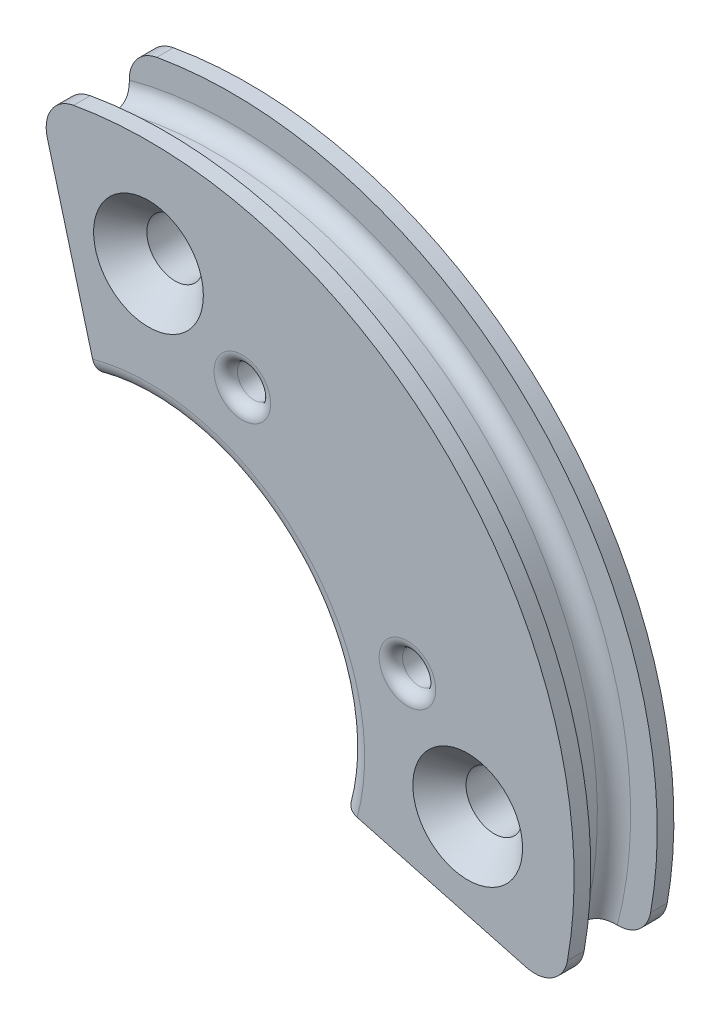
SolidWorks part; units mm, degrees
ref_plane "Front" through (0, 0, 0) normal (0, 0, 1) x (1, 0, 0)
ref_plane "Top" through (0, 0, 0) normal (0, 1, 0) x (1, 0, 0)
ref_plane "Right" through (0, 0, 0) normal (1, 0, 0) x (0, 0, -1)
sketch "Sketch1" plane through (0, 0, 0) normal (0, 0, 1) x (1, 0, 0)
  circle A2 centre (9.6, 0) radius 0.85
  circle A24 centre (0, 0) radius 12
  circle A25 centre (0, 0) radius 6
  circle A30 centre (0, -9.6) radius 0.85
  circle A32 centre (-9.6, 0) radius 0.85
  circle A34 centre (0, 9.6) radius 0.85
  point P20 (0, 0)
  dimension "D1" = 4
  dimension "D2" = 24
  dimension "D3" = 12
  dimension "D4" = 19.2
  dimension "D5" = 1.7
extrude "Boss-Extrude1" add sketch "Sketch1" along normal mid plane 3
sketch "Sketch2" plane through (0, 0, 0) normal (0, 1, 0) x (1, 0, 0)
  line L1 (0, 0) -> (0, 3.24) construction
  line L3 (-11.5, 0.5) -> (-11.5, -0.5)
  line L4 (-11.5, 0) -> (-12, 0) construction
  line L5 (-12, -1) -> (-12, 1)
  line L6 (-12, 1.5) -> (-12, -1.5) construction
  arc A1 (-12, 1) -> (-11.5, 0.5) centre (-12, 0.5) cw
  arc A2 (-12, -1) -> (-11.5, -0.5) centre (-12, -0.5) ccw
  dimension "D1" = 23
  dimension "D2" = 2
revolve "Cut-Revolve1" cut sketch "Sketch2" angle 360 about L1
sketch "Sketch6" plane through (0, 0, 0) normal (0, 1, 0) x (1, 0, 0)
  line L0 (0, 0) -> (15.0491, 0) construction
  line L1 (12, 1.5) -> (12.8, 1.5)
  line L2 (12, 1.5) -> (12, 1)
  line L3 (12, 1) -> (12.8, 1)
  line L4 (12.8, 1.5) -> (12.8, 1)
  line L5 (12.8, -1.5) -> (12.8, -1)
  line L6 (12, -1) -> (12.8, -1)
  line L7 (12, -1.5) -> (12, -1)
  line L8 (12, -1.5) -> (12.8, -1.5)
  line L9 (12, -1) -> (-12, -1) construction
  line L10 (0, 0) -> (0, 2.8804) construction
  arc A0 (11.5, -0.5) -> (12, -1) centre (12, -0.5) ccw construction
  dimension "D1" = 0.8
revolve "Revolve1" add sketch "Sketch6" angle 360 about L10
sketch "Sketch4" plane through (0, 0, 0) normal (0, 0, 1) x (1, 0, 0)
  line L0 (-3.7436, 13.9714) -> (0, 0)
  line L1 (0, 0) -> (8.4853, 8.4853) construction
  line L2 (0, 0) -> (-16.6927, 0) construction
  line L3 (14.9002, -3.9925) -> (0, 0)
  line L5 (-3.7436, 13.9714) -> (-15.1881, 13.9714)
  line L6 (-15.1881, 13.9714) -> (-15.1881, -14.8394)
  line L7 (-15.1881, -14.8394) -> (14.9002, -14.8394)
  line L10 (14.9002, -3.9925) -> (14.9002, -14.8394)
  point P15 (11.5911, -3.1058)
  point P18 (-3.1058, 11.5911)
  dimension "D3" = 60
  dimension "D1" = 135
  dimension "D2" = 120
extrude "Cut-Extrude1" cut sketch "Sketch4" against normal through all both and the other way through all
sketch "Sketch5" plane through (0, 0, 1.5) normal (0, 0, 1) x (1, 0, 0)
  line L1 (0, 0) -> (9.051, 9.051) construction
  circle A1 centre (2.8214, 7.7875) radius 0.5
  arc A2 (12.3639, -3.3129) -> (-3.3129, 12.3639) centre (0, 0) ccw construction
  circle A3 centre (7.7875, 2.8214) radius 0.5
  dimension "D1" = 1
extrude "Cut-Extrude2" cut sketch "Sketch5" against normal through all both and the other way through all
fillet "Fillet1" radius 0.5 2 edges at (4.2426, 4.2426, 1.5) (4.2426, 4.2426, -1.5)
fillet "Fillet2" radius 1 4 edges at (12.3639, -3.3129, -1.25) (12.3639, -3.3129, 1.25) (-3.3129, 12.3639, -1.25) (-3.3129, 12.3639, 1.25)
chamfer "Chamfer1" distance 0.8 angle 45 2 edges at (10.45, 0, 1.5) (0.85, 9.6, 1.5)
fillet "Fillet3" radius 0.35 2 edges at (3.3214, 7.7875, 1.5) (8.2875, 2.8214, 1.5)
fillet "Fillet4" radius 0.35 2 edges at (7.2875, 2.8214, -1.5) (3.3214, 7.7875, -1.5)
